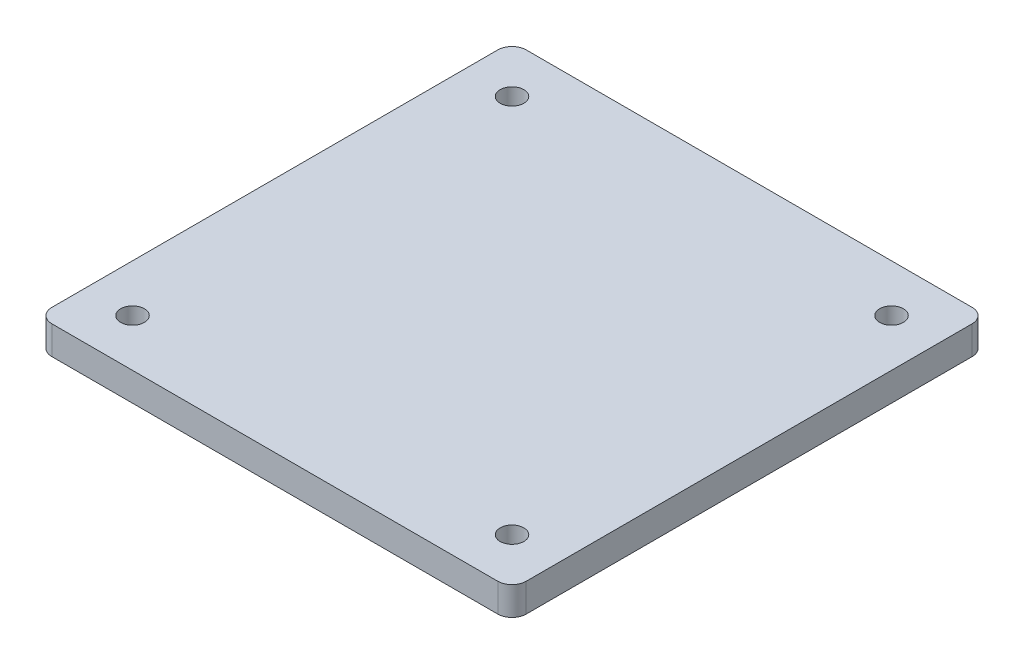
SolidWorks part; units mm, degrees
ref_plane "Front Plane" through (0, 0, 0) normal (0, 0, 1) x (1, 0, 0)
ref_plane "Top Plane" through (0, 0, 0) normal (0, 1, 0) x (1, 0, 0)
ref_plane "Right Plane" through (0, 0, 0) normal (1, 0, 0) x (0, 0, -1)
sketch "Sketch1" plane through (0, 0, 0) normal (0, 1, 0) x (1, 0, 0)
  line L1 (-10, 10) -> (90, 10)
  line L2 (-10, 10) -> (-10, -90)
  line L3 (-10, -90) -> (90, -90)
  line L4 (90, 10) -> (90, -90)
  circle A0 centre (0, 0) radius 2.5
  circle A1 centre (80, 0) radius 2.5
  circle A2 centre (80, -80) radius 2.5
  circle A3 centre (0, -80) radius 2.5
  dimension "D1" = 5
  dimension "D4" = 10
  dimension "D5" = 100
  dimension "D6" = 10
  dimension "D7" = 10
  dimension "D8" = 10
  dimension "D9" = 10
  dimension "D10" = 100
  dimension "D2" = 2
  dimension "D3" = 2
extrude "Boss-Extrude1" add sketch "Sketch1" along normal blind 6
fillet "Fillet1" radius 3 4 edges at (-10, 3, -10) (-10, 3, 90) (90, 3, -10) (90, 3, 90)
scale "Scale1" scale about centroid uniform scaling yes scale factor 7.5
